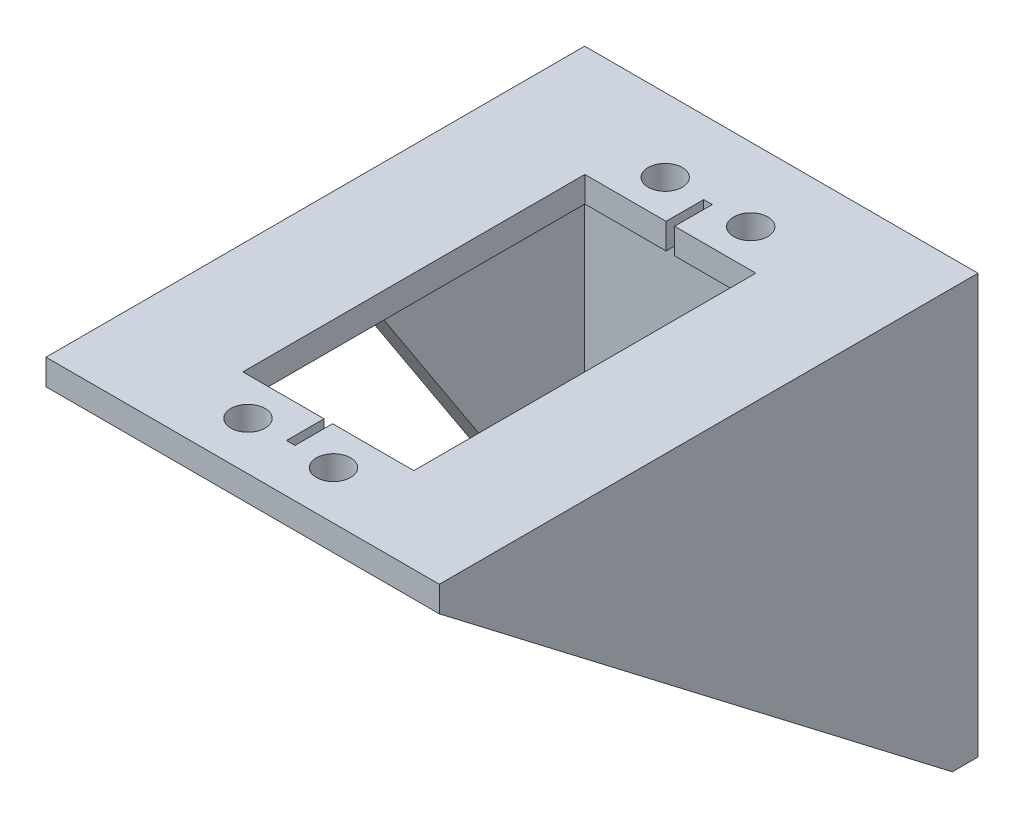
SolidWorks part; units mm, degrees
ref_plane "Front Plane" through (0, 0, 0) normal (0, 0, 1) x (1, 0, 0)
ref_plane "Top Plane" through (0, 0, 0) normal (0, 1, 0) x (1, 0, 0)
ref_plane "Right Plane" through (0, 0, 0) normal (1, 0, 0) x (0, 0, -1)
sketch "Sketch1" plane through (0, 0, 0) normal (0, 0, 1) x (1, 0, 0)
  line L0 (0, 0) -> (46, 0)
  line L1 (46, 0) -> (46, 46)
  line L2 (46, 46) -> (0, 46)
  line L3 (0, 46) -> (0, 0)
  line L4 (23, 23) -> (23, 0)
  line L5 (23, 23) -> (16, 23)
  line L6 (23, 23) -> (23, 30)
  line L7 (23, 23) -> (30, 23)
  line L8 (23, 23) -> (23, 16)
  circle A0 centre (23, 23) radius 3
  circle A1 centre (30, 23) radius 0.75
  circle A2 centre (23, 30) radius 0.75
  circle A3 centre (16, 23) radius 0.75
  circle A4 centre (23, 16) radius 0.75
extrude "Boss-Extrude1" add sketch "Sketch1" along normal blind 3
sketch "Sketch2" plane through (0, 0, 3) normal (0, 0, 1) x (1, 0, 0)
  line L0 (0, 46) -> (0, 49)
  line L1 (0, 49) -> (46, 49)
  line L2 (46, 49) -> (46, 46)
  line L3 (0, 46) -> (46, 46)
extrude "Boss-Extrude2" add sketch "Sketch2" along normal blind 60 and the other way blind 3
sketch "Sketch3" plane through (0, 46, 0) normal (0, -1, 0) x (-1, 0, 0)
  line L0 (-46, -3) -> (-33, -3)
  line L1 (-46, -3) -> (0, -3) construction
  line L2 (-33, -3) -> (-13, -3)
  line L3 (-33, -3) -> (-28, -3)
  line L4 (-28, -3) -> (-18, -3)
  line L5 (-18, -3) -> (-18, -6.0811)
  line L6 (-18, -6.0811) -> (-18, -8.5811)
  line L7 (-18, -8.5811) -> (-28, -8.5811)
  line L8 (-23, -8.5811) -> (-22.5, -8.5811)
  line L9 (-23, -8.5811) -> (-23.5, -8.5811)
  line L10 (-23.5, -8.5811) -> (-23.5, -12.9811)
  line L11 (-23.5, -12.9811) -> (-22.5, -12.9811)
  line L12 (-22.5, -12.9811) -> (-22.5, -8.5811)
  line L13 (-22.5, -12.9811) -> (-13, -12.9811)
  line L14 (-23.5, -12.9811) -> (-33, -12.9811)
  line L15 (-33, -12.9811) -> (-33, -52.9811)
  line L16 (-33, -32.9811) -> (-13, -32.9811)
  line L17 (-13, -52.9811) -> (-13, -12.9811)
  line L18 (-23.5, -52.9811) -> (-33, -52.9811)
  line L19 (-22.5, -52.9811) -> (-13, -52.9811)
  line L20 (-22.5, -52.9811) -> (-22.5, -57.3811)
  line L21 (-23.5, -52.9811) -> (-22.5, -52.9811)
  line L22 (-23.5, -57.3811) -> (-23.5, -52.9811)
  line L23 (-23, -57.3811) -> (-23.5, -57.3811)
  line L24 (-23, -57.3811) -> (-22.5, -57.3811)
  line L25 (-18, -57.3811) -> (-28, -57.3811)
  line L26 (-18, -59.8811) -> (-18, -57.3811)
  circle A0 centre (-18, -8.5811) radius 2
  circle A1 centre (-28, -8.5811) radius 2
  circle A2 centre (-28, -57.3811) radius 2
  circle A3 centre (-18, -57.3811) radius 2
  dimension "D3" = 10
  dimension "D1" = 20
  dimension "D2" = 13
extrude "Cut-Extrude1" cut sketch "Sketch3" against normal blind 10
sketch "Sketch4" plane through (0, 46, 0) normal (0, -1, 0) x (-1, 0, 0)
  line L0 (0, -3) -> (-3, -3)
  line L1 (0, -3) -> (-46, -3) construction
  line L2 (-3, -3) -> (-3, -63)
  line L3 (0, -63) -> (-46, -63) construction
  line L4 (-3, -63) -> (0, -63)
  line L5 (0, -63) -> (0, -3)
  line L6 (-46, -3) -> (-43, -3)
  line L7 (-43, -3) -> (-43, -63)
  line L8 (-43, -63) -> (-46, -63)
  line L9 (-46, -63) -> (-46, -3)
  line L10 (-3, -33) -> (0, -33)
  line M24 (0, -3) -> (-46, -3)
  line M25 (-46, -3) -> (-46, -63)
  line M26 (-46, -63) -> (0, -63)
extrude "Boss-Extrude3" add sketch "Sketch4" along normal blind 46 contours L7 M24 M25 M26 | L2 L10 L5 M24
sketch "Sketch5" plane through (43, 0, 0) normal (-1, 0, 0) x (0, 0, 1)
  line L0 (63, 46) -> (3, 0)
  line L1 (3, 0) -> (63, 0)
  line L2 (63, 0) -> (63, 46)
extrude "Cut-Extrude2" cut sketch "Sketch5" against normal blind 46 and the other way blind 46
sketch "Sketch6" plane through (0, 0, 0) normal (-1, 0, 0) x (0, 0, 1)
  line L0 (3, 0) -> (33, 46)
  line L1 (3, 46) -> (63, 46) construction
  line L2 (33, 46) -> (33, 23)
  line L3 (3, 0) -> (63, 46) construction
  line L4 (33, 23) -> (3, 0)
extrude "Cut-Extrude3" cut sketch "Sketch6" against normal blind 15
sketch "Sketch7" plane through (0, 0, 3) normal (0, 0, 1) x (1, 0, 0)
  line L0 (43, 46) -> (34, 46)
  line L1 (43, 46) -> (3, 46) construction
  line L2 (34, 46) -> (34, 37)
  line L3 (34, 37) -> (38.5, 37)
  line L4 (38.5, 37) -> (38.5, 40)
  line L5 (38.5, 40) -> (29.5, 40)
  line L6 (29.5, 40) -> (29.5, 37)
  line L7 (29.5, 37) -> (34, 37)
extrude "Cut-Extrude4" cut sketch "Sketch7" against normal blind 10 contours L4 L5 L2 L3 | L6 L7 L2 L5
